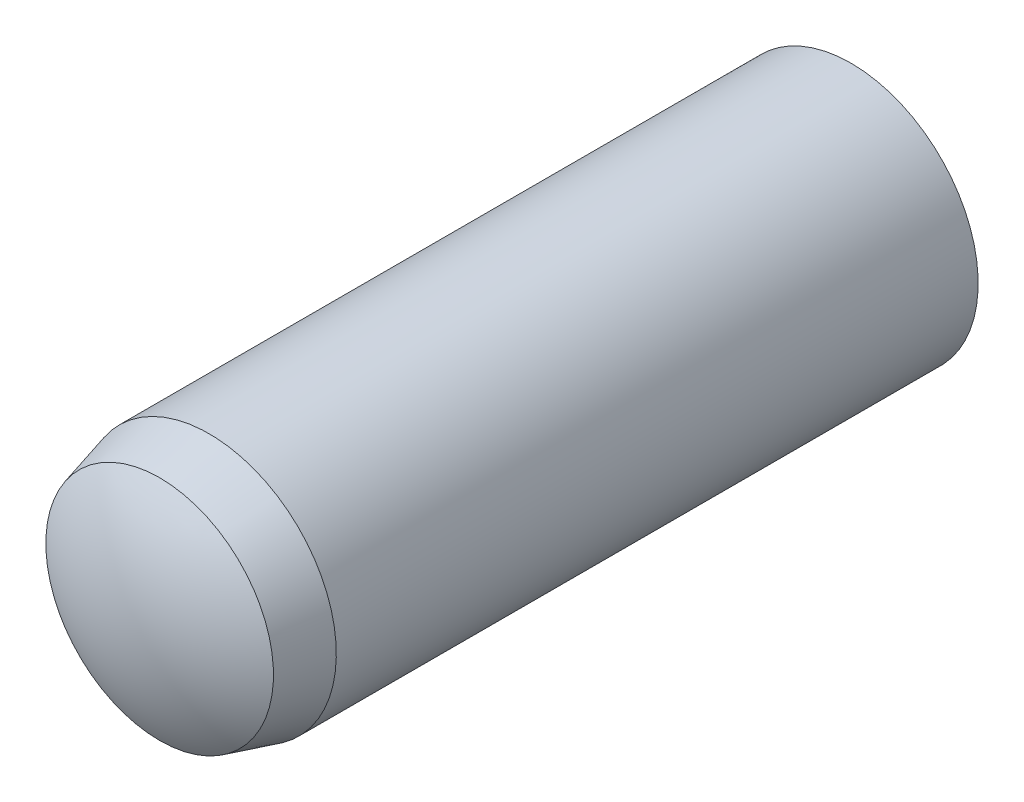
SolidWorks part; units mm, degrees
material "Plain Carbon Steel"
ref_plane "Front Plane" through (0, 0, 0) normal (0, 0, 1) x (1, 0, 0)
ref_plane "Top Plane" through (0, 0, 0) normal (0, 1, 0) x (1, 0, 0)
ref_plane "Right Plane" through (0, 0, 0) normal (1, 0, 0) x (0, 0, -1)
sketch "Sketch1" plane through (0, 0, 0) normal (0, 0, 1) x (1, 0, 0)
  circle A0 centre (0, 0) radius 2
  point P3 (0, 2)
  dimension "Diameter" = 4
sketch "Sketch2" plane through (0, 0, 0) normal (1, 0, 0) x (0, 0, -1)
  line L0 (-6, 0) -> (6, 0) construction
  line L1 (-6, 0) -> (-6, 2) construction
  line L2 (-6, 2) -> (6, 2)
  line L3 (6, 2) -> (6, 0) construction
  line L4 (-5.48, 1.791) -> (-4.7, 2)
  arc A0 (-6, 0) -> (-5.48, 1.791) centre (-2.6557, 0) cw
  arc A1 (6, 0) -> (5.4, 2) centre (2.3667, 0) ccw
  point P2 (0, 0)
  point P11 (-2, 0)
  point P13 (2, 0)
  dimension "Length" = 12
  dimension "D1" = 15
  dimension "D2" = 0.6
  dimension "D3" = 1.3
  dimension "D4" = 0.78
  dimension "D5" = 4
  dimension "D6" = 4
sketch "Sketch3" plane through (0, 0, 0) normal (1, 0, 0) x (0, 0, -1)
  line L0 (-6, 0) -> (6, 0) construction
  line L1 (-5.48, 1.791) -> (-4.7, 2) construction
  line L2 (-6, 0) -> (6, 0)
  line L3 (-5.48, 1.791) -> (-4.7, 2)
  line L4 (-4.7, 2) -> (5.4, 2)
  arc A0 (6, 0) -> (5.4, 2) centre (2.3667, 0) ccw construction
  arc A1 (-5.48, 1.791) -> (-6, 0) centre (-2.6557, 0) ccw construction
  arc A2 (6, 0) -> (5.4, 2) centre (2.3667, 0) ccw
  arc A3 (-5.48, 1.791) -> (-6, 0) centre (-2.6557, 0) ccw
revolve "Revolve1" add sketch "Sketch3" angle 360 about L2
equation "\"D2@Sketch2\" = \"Diameter@Sketch1\" * .15"
equation "\"D3@Sketch2\" = \"Diameter@Sketch1\" * .325"
equation "\"D4@Sketch2\" = \"D3@Sketch2\" * .6"
equation "\"D5@Sketch2\"=\"Diameter@Sketch1\""
equation "\"D6@Sketch2\"=\"D5@sketch2\""
